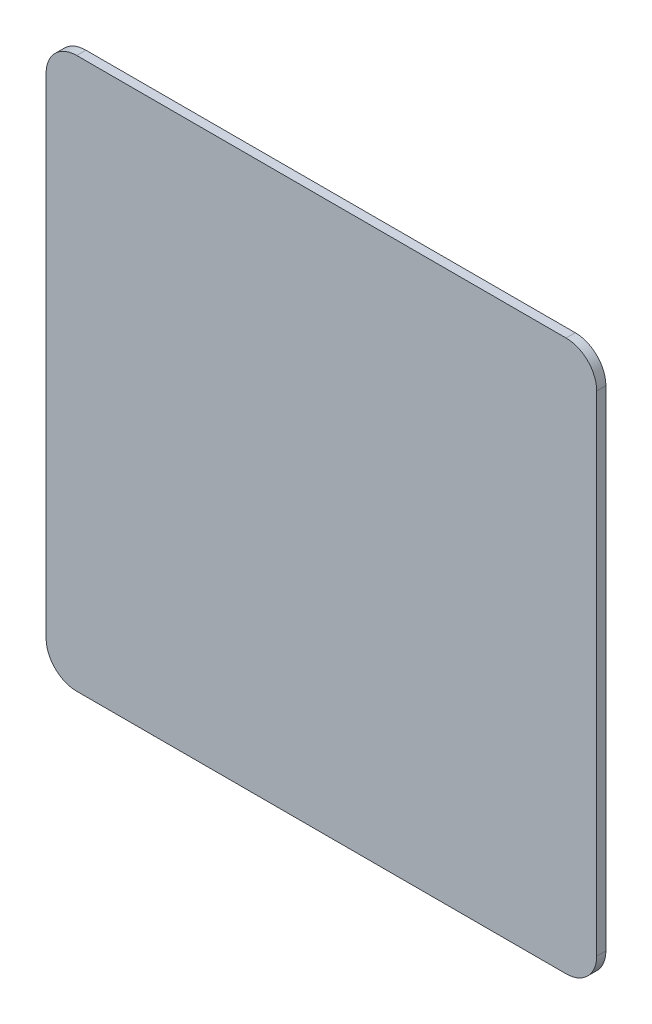
SolidWorks part; units mm, degrees
ref_plane "Piano frontale" through (0, 0, 0) normal (0, 0, 1) x (1, 0, 0)
ref_plane "Piano superiore" through (0, 0, 0) normal (0, 1, 0) x (1, 0, 0)
ref_plane "Piano destro" through (0, 0, 0) normal (1, 0, 0) x (0, 0, -1)
sketch "Sketch1" plane through (0, 0, 0) normal (0, 0, 1) x (1, 0, 0)
  line L8 (-90, 80) -> (-90, -80)
  line L9 (-80, -90) -> (80, -90)
  line L10 (90, -80) -> (90, 80)
  line L11 (80, 90) -> (-80, 90)
  arc A8 (-80, 90) -> (-90, 80) centre (-80, 80) ccw
  arc A9 (-90, -80) -> (-80, -90) centre (-80, -80) ccw
  arc A10 (80, -90) -> (90, -80) centre (80, -80) ccw
  arc A11 (90, 80) -> (80, 90) centre (80, 80) ccw
extrude "Boss-Extrude1" add sketch "Sketch1" along normal blind 3
